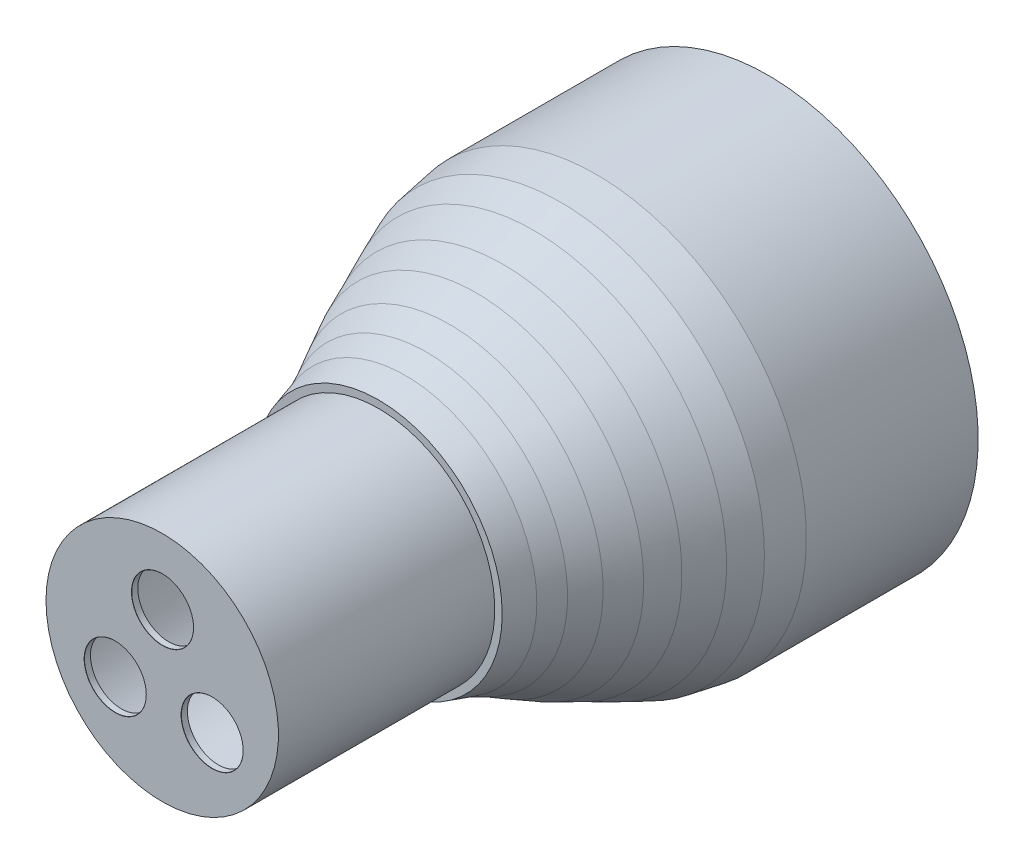
SolidWorks part; units mm, degrees
ref_plane "Front Plane" through (0, 0, 0) normal (0, 0, 1) x (1, 0, 0)
ref_plane "Top Plane" through (0, 0, 0) normal (0, 1, 0) x (1, 0, 0)
ref_plane "Right Plane" through (0, 0, 0) normal (1, 0, 0) x (0, 0, -1)
sketch "ff" plane through (0, 0, 0) normal (0, 1, 0) x (1, 0, 0)
  line L6 (-27.469, 50) -> (-28.669, 50)
  line L10 (-42.669, 113) -> (-42.669, 93)
  line L12 (-42.669, 93) -> (-42.669, 90.3333)
  line L13 (-42.669, 90.3333) -> (-42.669, 85.2089)
  line L14 (-42.669, 85.2089) -> (-41.669, 79.4226)
  line L15 (-41.669, 79.4226) -> (-39.8624, 75.1172)
  line L16 (-39.8624, 75.1172) -> (-37.6189, 70.1225)
  line L17 (-37.6189, 70.1225) -> (-35.7524, 65.8116)
  line L18 (-35.7524, 65.8116) -> (-33.4895, 61.5062)
  line L19 (-33.4895, 61.5062) -> (-31.4683, 57.7775)
  line L20 (-31.4683, 57.7775) -> (-29.9329, 54.3357)
  line L21 (-29.9329, 54.3357) -> (-28.669, 50)
  line L23 (-42.669, 113) -> (-41.669, 113)
  line L24 (-41.669, 113) -> (-41.669, 93)
  line L25 (-41.669, 93) -> (-39.3715, 77.8398)
  line L27 (-39.3715, 77.8398) -> (-34.0769, 65.8116)
  line L28 (-34.0769, 65.8116) -> (-29.9329, 59.3264)
  line L29 (-29.9329, 59.3264) -> (-27.0949, 53.9341)
  line L33 (-27.0949, 53.9341) -> (-26.469, 50)
  line L38 (-27.469, 50) -> (-27.469, 15)
  line L39 (-26.469, 50) -> (-26.469, 16)
  line L43 (-27.469, 15) -> (-8.669, 15)
  line L44 (-26.469, 16) -> (-8.669, 16)
  line L45 (-8.669, 16) -> (-8.669, 15)
  dimension "D1" = 35
  dimension "D2" = 1
  dimension "D3" = 34
  dimension "D4" = 18.8
  dimension "D5" = 20
  dimension "D6" = 17.8
  dimension "D7" = 1
  dimension "D8" = 20
  dimension "D9" = 33
revolve "Revolve1" add sketch "ff" angle 360 about L45
hole_wizard "Ø10.0mm Dowel Hole1" positions "Sketch1" profile "Sketch2" hole size "Ø10.0" standard "ANSI Metric" end condition through all
sketch "Sketch1" plane through (0, 0, -15) normal (0, 0, 1) x (1, 0, 0)
  point P0 (-8.6218, 8.1223)
  point P2 (-16.2719, -5.1001)
  point P4 (-0.5939, -5.1001)
sketch "Sketch2" plane through (-8.6218, 8.1223, -15) normal (1, 0, 0) x (0, -1, 0)
  line L0 (0, 0) -> (0, 98)
  line L1 (0, 98) -> (5, 98)
  line L2 (5, 98) -> (5, 0.025)
  line L3 (5, 0.025) -> (5.025, 0)
  line L5 (5.025, 0) -> (0, 0)
  line L6 (-5, 0.025) -> (-5.025, 0) construction
  line L11 (0, -6.35) -> (0, 107.95) construction
  dimension "Thru Hole Dia." = 10
  dimension "Thru Hole Depth" = 98
  dimension "Near C'Sink Dia." = 10.05
  dimension "Near C'Sink Angle" = 90
